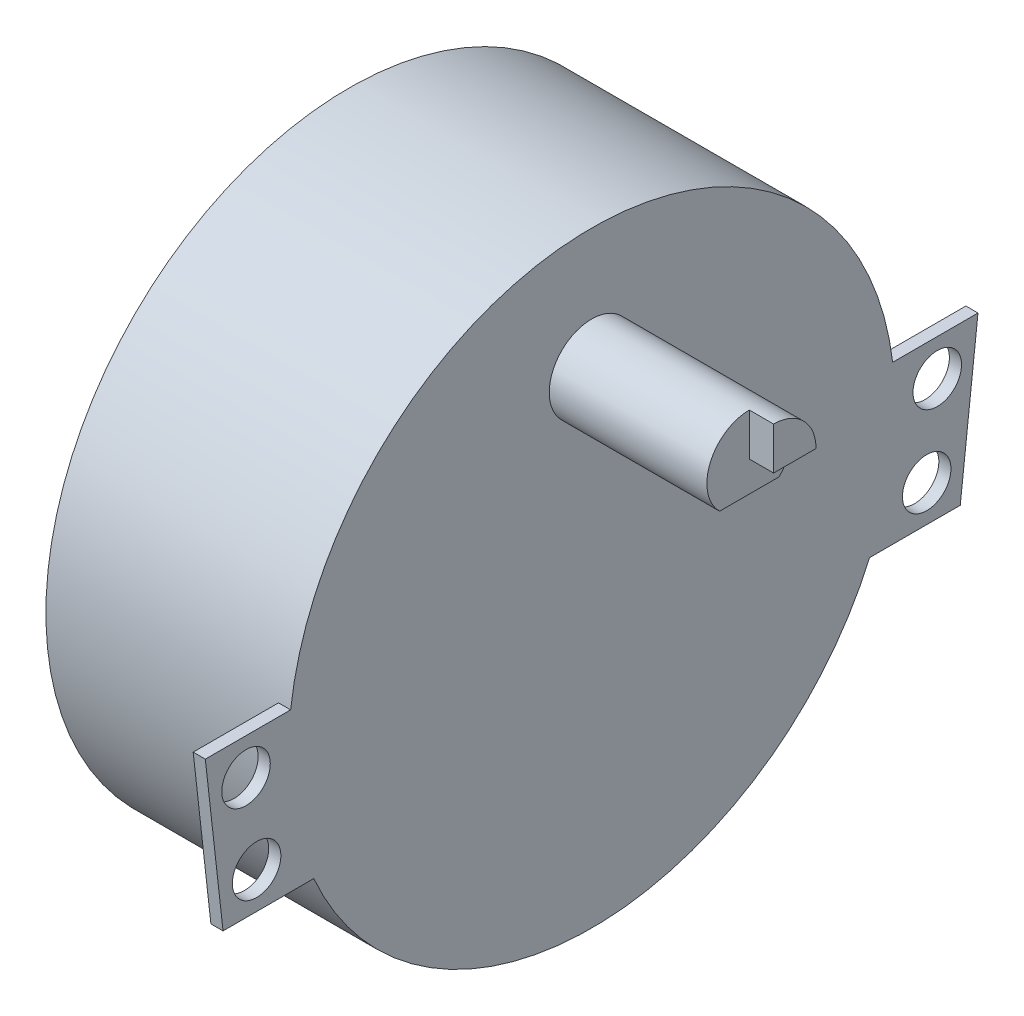
SolidWorks part; units mm, degrees
ref_plane "Front Plane" through (0, 0, 0) normal (0, 0, 1) x (1, 0, 0)
ref_plane "Top Plane" through (0, 0, 0) normal (0, 1, 0) x (1, 0, 0)
ref_plane "Right Plane" through (0, 0, 0) normal (1, 0, 0) x (0, 0, -1)
sketch "Sketch1" plane through (0, 0, 0) normal (1, 0, 0) x (0, 0, -1)
  circle A0 centre (0, 0) radius 25
extrude "Boss-Extrude1" add sketch "Sketch1" along normal blind 20
sketch "Sketch2" plane through (20, 0, 0) normal (1, 0, 0) x (0, 0, -1)
  line L2 (-2.4495, 12.5) -> (2.4495, 12.5)
  arc A1 (2.4495, 12.5) -> (-2.4495, 12.5) centre (0, 15) ccw
  dimension "D1" = 15
extrude "Boss-Extrude2" add sketch "Sketch2" along normal blind 15
sketch "Sketch3" plane through (20, 0, 0) normal (1, 0, 0) x (0, 0, -1)
  line L0 (-31.8547, 3) -> (-30.3928, -10)
  line L1 (31.8547, 3) -> (30.3928, -10)
  line L2 (-31.8547, 3) -> (-24.8193, 3)
  line L4 (-30.3928, -10) -> (-22.9129, -10)
  line L5 (30.3928, -10) -> (22.9129, -10)
  line L6 (31.8547, 3) -> (24.8193, 3)
  circle A2 centre (-28.4978, 0) radius 2
  arc A3 (-24.8193, 3) -> (-22.9129, -10) centre (0, 0) ccw
  circle A4 centre (-27.6248, -7) radius 2
  circle A5 centre (27.6248, -7) radius 2
  arc A6 (24.8193, 3) -> (22.9129, -10) centre (0, 0) cw
  circle A7 centre (28.4978, 0) radius 2
  dimension "D1" = 7
extrude "Boss-Extrude3" add sketch "Sketch3" against normal blind 1
sketch "Sketch4" plane through (35, 0, 0) normal (1, 0, 0) x (0, 0, -1)
  line L0 (0, 15) -> (3.5, 15)
  line L1 (0, 15) -> (0, 18.5)
  arc A0 (2.4495, 12.5) -> (-2.4495, 12.5) centre (0, 15) ccw construction
  arc A2 (0, 18.5) -> (3.5, 15) centre (0, 15) ccw
extrude "Cut-Extrude1" cut sketch "Sketch4" against normal blind 2
